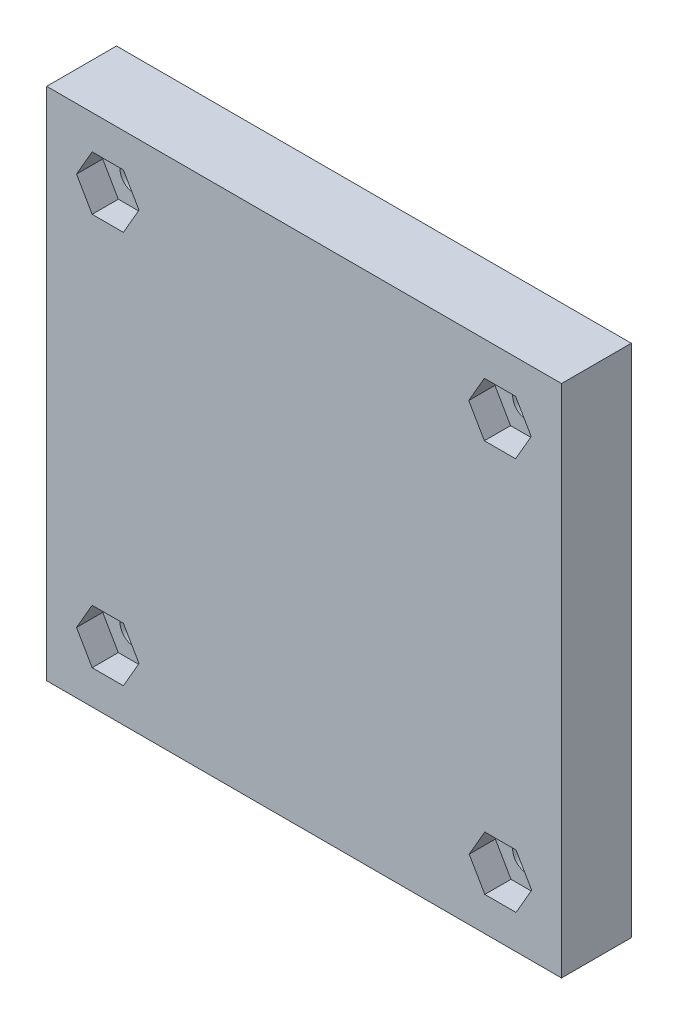
SolidWorks part; units mm, degrees
ref_plane "Ebene vorne" through (0, 0, 0) normal (0, 0, 1) x (1, 0, 0)
ref_plane "Ebene oben" through (0, 0, 0) normal (0, 1, 0) x (1, 0, 0)
ref_plane "Ebene rechts" through (0, 0, 0) normal (1, 0, 0) x (0, 0, -1)
sketch "Skizze1" plane through (0, 0, 0) normal (0, 0, 1) x (1, 0, 0)
  line L1 (-29.5, 29.5) -> (29.5, 29.5)
  line L2 (-29.5, 29.5) -> (-29.5, -29.5)
  line L3 (-29.5, -29.5) -> (29.5, -29.5)
  line L4 (29.5, 29.5) -> (29.5, -29.5)
  dimension "D3" = 29.5
  dimension "D1" = 59
  dimension "D2" = 59
  dimension "D4" = 29.5
extrude "Aufsatz-Linear austragen1" add sketch "Skizze1" along normal blind 8
sketch "Skizze2" plane through (0, 0, 0) normal (0, 0, 1) x (1, 0, 0)
  line L1 (27.5, 27.5) -> (-27.5, 27.5)
  line L2 (27.5, 27.5) -> (27.5, -27.5)
  line L3 (27.5, -27.5) -> (-27.5, -27.5)
  line L4 (-27.5, 27.5) -> (-27.5, -27.5)
  dimension "D1" = 55
  dimension "D2" = 55
  dimension "D3" = 27.5
  dimension "D4" = 27.5
sketch "Skizze3" plane through (0, 0, 0) normal (0, 0, 1) x (1, 0, 0)
  line L0 (27.5, -27.5) -> (-27.5, -27.5) construction
  line L1 (27.5, 27.5) -> (27.5, -27.5) construction
  line L2 (-27.5, 27.5) -> (-27.5, -27.5) construction
  line L3 (27.5, 27.5) -> (-27.5, 27.5) construction
  circle A0 centre (22.5, 22.5) radius 1.6
  circle A1 centre (-22.5, 22.5) radius 1.6
  circle A2 centre (-22.5, -22.5) radius 1.6
  circle A3 centre (22.5, -22.5) radius 1.6
  dimension "D1" = 3.2
  dimension "D2" = 3.2
  dimension "D3" = 3.2
  dimension "D4" = 3.2
  dimension "D5" = 5
  dimension "D6" = 5
  dimension "D7" = 5
  dimension "D8" = 5
  dimension "D9" = 5
  dimension "D10" = 5
  dimension "D11" = 5
  dimension "D12" = 5
extrude "Schnitt-Linear austragen6" [suppressed] cut sketch "Skizze2" along normal blind 2
shell "Wandung4" thickness 2
sketch "Skizze5" plane through (0, 0, 6) normal (0, 0, -1) x (-1, 0, 0)
  line L1 (-27.5, 27.5) -> (-17.5, 27.5)
  line L2 (-27.5, 27.5) -> (-27.5, 17.5)
  line L3 (-27.5, 17.5) -> (-17.5, 17.5)
  line L4 (-17.5, 27.5) -> (-17.5, 17.5)
  line L5 (27.5, 27.5) -> (17.5, 27.5)
  line L6 (27.5, 27.5) -> (27.5, 17.5)
  line L7 (27.5, 17.5) -> (17.5, 17.5)
  line L8 (17.5, 27.5) -> (17.5, 17.5)
  line L9 (-27.5, -27.5) -> (-17.5, -27.5)
  line L10 (-27.5, -27.5) -> (-27.5, -17.5)
  line L11 (-27.5, -17.5) -> (-17.5, -17.5)
  line L12 (-17.5, -27.5) -> (-17.5, -17.5)
  line L13 (27.5, -27.5) -> (17.5, -27.5)
  line L14 (27.5, -27.5) -> (27.5, -17.5)
  line L15 (27.5, -17.5) -> (17.5, -17.5)
  line L16 (17.5, -27.5) -> (17.5, -17.5)
  dimension "D1" = 10
  dimension "D2" = 10
  dimension "D3" = 10
  dimension "D4" = 10
  dimension "D5" = 10
  dimension "D6" = 10
  dimension "D7" = 10
  dimension "D8" = 10
extrude "Aufsatz-Linear austragen2" add sketch "Skizze5" along normal blind 4
extrude "Schnitt-Linear austragen8" cut sketch "Skizze3" along normal blind 10
sketch "Skizze6" plane through (-29.5, 0, 0) normal (-1, 0, 0) x (0, 0, 1)
  line L0 (8, 29.5) -> (8, -29.5) construction
  line L1 (2.5, 9.5) -> (6, 9.5)
  line L2 (2.5, 9.5) -> (2.5, -0.5)
  line L3 (2.5, -0.5) -> (6, -0.5)
  line L4 (6, 9.5) -> (6, -0.5)
  line L5 (0, 29.5) -> (0, -29.5) construction
  line L6 (8, 29.5) -> (0, 29.5) construction
  dimension "D1" = 2
  dimension "D2" = 3.5
  dimension "D3" = 10
  dimension "D4" = 20
  dimension "D5" = 2.5
extrude "Schnitt-Linear austragen10" cut sketch "Skizze6" against normal blind 2
sketch "Skizze7" plane through (0, 0, 8) normal (0, 0, 1) x (1, 0, 0)
  line L0 (29.5, 29.5) -> (-29.5, 29.5) construction
  line L1 (-20.7102, 25.6) -> (-24.2898, 25.6)
  line L2 (-24.2898, 25.6) -> (-26.0796, 22.5)
  line L3 (-26.0796, 22.5) -> (-24.2898, 19.4)
  line L4 (-24.2898, 19.4) -> (-20.7102, 19.4)
  line L5 (-20.7102, 19.4) -> (-18.9204, 22.5)
  line L6 (-18.9204, 22.5) -> (-20.7102, 25.6)
  line L7 (-29.5, -29.5) -> (29.5, -29.5) construction
  line L8 (24.2379, 25.6) -> (20.6583, 25.6)
  line L9 (20.6583, 25.6) -> (18.8685, 22.5)
  line L10 (18.8685, 22.5) -> (20.6583, 19.4)
  line L11 (20.6583, 19.4) -> (24.2379, 19.4)
  line L12 (24.2379, 19.4) -> (26.0277, 22.5)
  line L13 (26.0277, 22.5) -> (24.2379, 25.6)
  line L14 (-18.9204, -22.5) -> (-20.7102, -19.4)
  line L15 (-20.7102, -19.4) -> (-24.2898, -19.4)
  line L16 (-24.2898, -19.4) -> (-26.0796, -22.5)
  line L17 (-26.0796, -22.5) -> (-24.2898, -25.6)
  line L18 (-24.2898, -25.6) -> (-20.7102, -25.6)
  line L19 (-20.7102, -25.6) -> (-18.9204, -22.5)
  line L20 (24.2898, -19.4) -> (20.7102, -19.4)
  line L21 (20.7102, -19.4) -> (18.9204, -22.5)
  line L22 (18.9204, -22.5) -> (20.7102, -25.6)
  line L23 (20.7102, -25.6) -> (24.2898, -25.6)
  line L24 (24.2898, -25.6) -> (26.0796, -22.5)
  line L25 (26.0796, -22.5) -> (24.2898, -19.4)
  circle A0 centre (-22.5, 22.5) radius 3.1 construction
  circle A1 centre (22.4481, 22.5) radius 3.1 construction
  circle A2 centre (-22.5, -22.5) radius 3.1 construction
  circle A3 centre (22.5, -22.5) radius 3.1 construction
  dimension "D1" = 6.2
  dimension "D2" = 6.2
  dimension "D3" = 6.2
  dimension "D4" = 6.2
extrude "Schnitt-Linear austragen11" cut sketch "Skizze7" against normal blind 3
